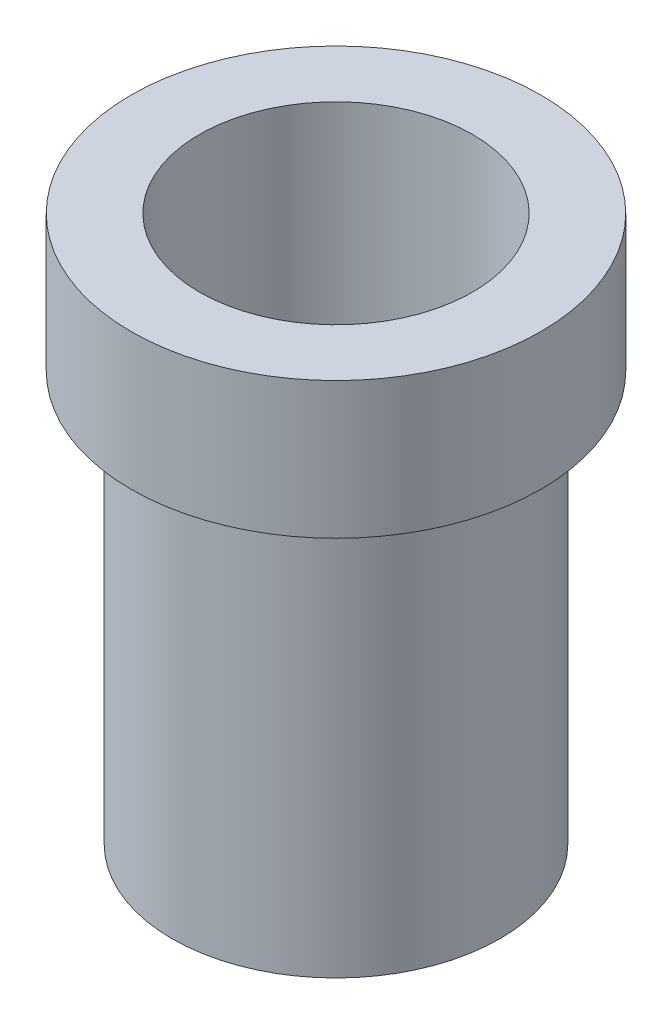
SolidWorks part; units mm, degrees
ref_plane "Face" through (0, 0, 0) normal (0, 0, 1) x (1, 0, 0)
ref_plane "Dessus" through (0, 0, 0) normal (0, 1, 0) x (1, 0, 0)
ref_plane "Droite" through (0, 0, 0) normal (1, 0, 0) x (0, 0, -1)
sketch "Esquisse1" plane through (0, 0, 0) normal (0, 1, 0) x (1, 0, 0)
  circle A0 centre (0, 0) radius 7.5
  dimension "D1" = 15
extrude "Extrusion1" add sketch "Esquisse1" along normal blind 5
sketch "Esquisse2" plane through (0, 0, 0) normal (0, -1, 0) x (1, 0, 0)
  circle A0 centre (0, 0) radius 6
  dimension "D1" = 12
extrude "Extrusion2" add sketch "Esquisse2" along normal blind 15
sketch "Esquisse3" plane through (0, 5, 0) normal (0, 1, 0) x (1, 0, 0)
  circle A0 centre (0, 0) radius 5
  dimension "D1" = 10
extrude "Extrusion3" cut sketch "Esquisse3" against normal up to next
